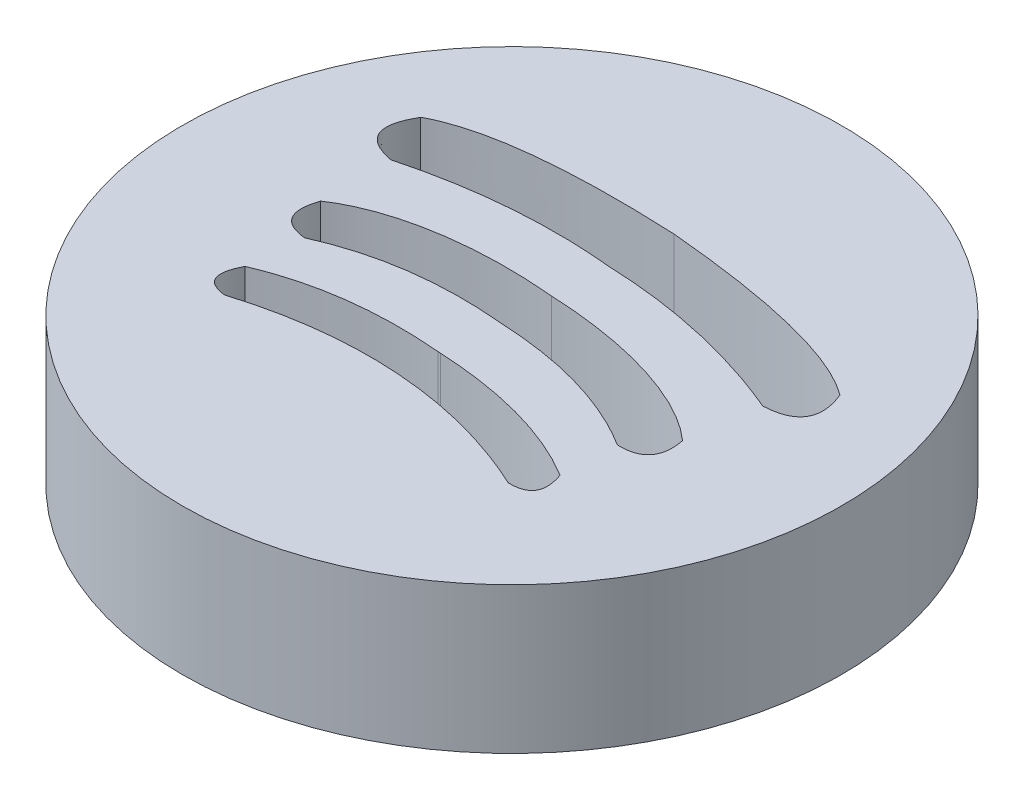
SolidWorks part; units mm, degrees
ref_plane "Front Plane" through (0, 0, 0) normal (0, 0, 1) x (1, 0, 0)
ref_plane "Top Plane" through (0, 0, 0) normal (0, 1, 0) x (1, 0, 0)
ref_plane "Right Plane" through (0, 0, 0) normal (1, 0, 0) x (0, 0, -1)
sketch "Sketch1" plane through (0, 0, 0) normal (0, 1, 0) x (1, 0, 0)
  line L0 (170.6667, 512) -> (853.3333, 512) construction
  line L1 (0.3505, 0.1387) -> (9.344, 9.1322) construction
  line L2 (0.3505, 9.1322) -> (9.344, 0.1387) construction
  line L3 (4.8473, 4.6354) -> (4.4544, 0.1417) construction
  line L4 (4.8473, 4.6354) -> (5.1552, 9.1357) construction
  line L5 (4.7658, 3.7042) -> (4.8011, 3.7017)
  line L6 (4.7189, 3.1672) -> (4.7744, 3.1634)
  line L7 (4.8331, 4.4735) -> (4.8392, 4.473)
  circle A0 centre (4.8473, 4.6354) radius 4.5108
  spline S0 degree 2 poles (4.9894, 6.7126) (2.7085, 6.8193) (1.87, 6.3624) knots 0 0 0 1 1 1
  spline S1 degree 2 poles (1.87, 6.3624) (1.5297, 5.7756) (2.1725, 5.6546) knots 0 0 0 1 1 1
  spline S2 degree 2 poles (2.1725, 5.6546) (3.5394, 6.0211) (4.9326, 5.8825) knots 0 0 0 1 1 1
  spline S3 degree 3 poles (4.8818, 5.14) (3.6273, 5.2563) (2.6897, 5.0307) (2.1801, 4.6855) knots 0 0 0 0 1 1 1 1
  spline S4 degree 2 poles (2.1801, 4.6855) (2.0116, 4.1918) (2.5031, 4.1389) knots 0 0 0 1 1 1
  spline S5 degree 2 poles (2.5031, 4.1389) (3.5189, 4.5963) (4.8331, 4.4735) knots 0 0 0 1 1 1
  spline S6 degree 2 poles (4.7658, 3.7042) (3.4298, 3.8207) (2.4355, 3.3922) knots 0 0 0 1 1 1
  spline S7 degree 2 poles (2.4355, 3.3922) (2.2118, 2.9596) (2.6352, 2.9143) knots 0 0 0 1 1 1
  spline S8 degree 2 poles (2.6352, 2.9143) (3.6835, 3.2365) (4.7189, 3.1672) knots 0 0 0 1 1 1
  spline S9 degree 2 poles (6.8043, 2.629) (5.8096, 3.091) (4.7744, 3.1634) knots 0 0 0 1 1 1
  spline S10 degree 2 poles (7.0671, 3.0752) (7.2299, 2.6162) (6.8043, 2.629) knots 0 0 0 1 1 1
  spline S11 degree 2 poles (4.8011, 3.7017) (6.1405, 3.6352) (7.0671, 3.0752) knots 0 0 0 1 1 1
  spline S12 degree 2 poles (7.102, 3.8242) (6.1579, 4.4157) (4.8392, 4.473) knots 0 0 0 1 1 1
  spline S13 degree 2 poles (7.4964, 4.3217) (7.5961, 3.8097) (7.102, 3.8242) knots 0 0 0 1 1 1
  spline S14 degree 3 poles (4.8818, 5.14) (6.1404, 5.0843) (7.0386, 4.733) (7.4964, 4.3217) knots 0 0 0 0 1 1 1 1
  spline S15 degree 2 poles (7.6359, 5.2807) (6.3317, 5.83) (4.9326, 5.8825) knots 0 0 0 1 1 1
  spline S16 degree 2 poles (8.032, 5.9407) (8.2892, 5.313) (7.6359, 5.2807) knots 0 0 0 1 1 1
  spline S17 degree 2 poles (4.9894, 6.7126) (7.2636, 6.5076) (8.032, 5.9407) knots 0 0 0 1 1 1
extrude "Boss-Extrude1" add sketch "Sketch1" along normal blind 2
